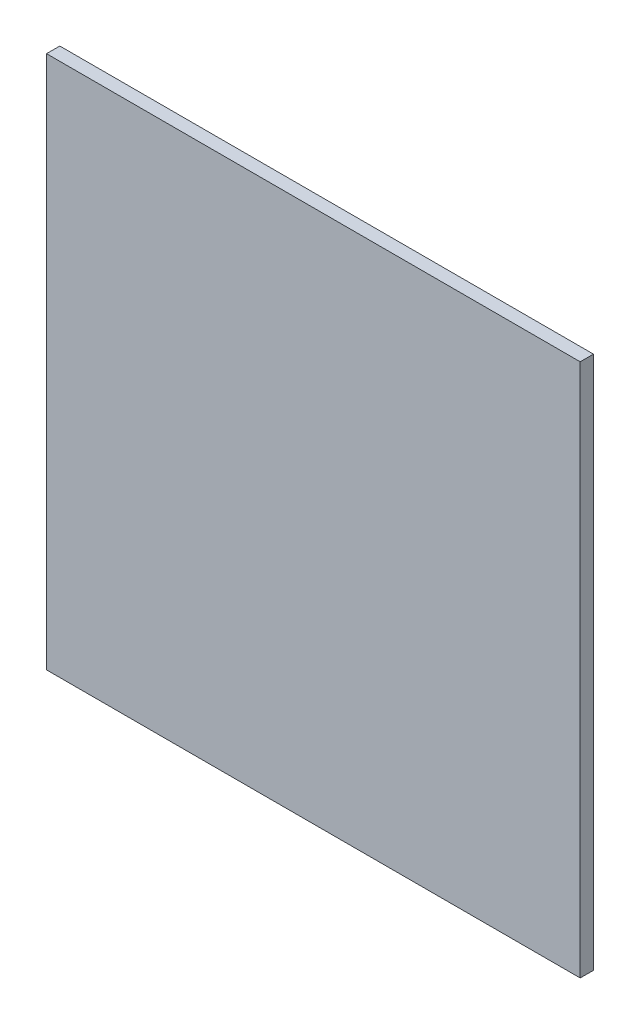
SolidWorks part; units mm, degrees
ref_plane "Front Plane" through (0, 0, 0) normal (0, 0, 1) x (1, 0, 0)
ref_plane "Top Plane" through (0, 0, 0) normal (0, 1, 0) x (1, 0, 0)
ref_plane "Right Plane" through (0, 0, 0) normal (1, 0, 0) x (0, 0, -1)
sketch "Sketch1" plane through (0, 0, 0) normal (0, 0, 1) x (1, 0, 0)
  line L1 (-63.881, -63.881) -> (63.881, -63.881)
  line L2 (-63.881, -63.881) -> (-63.881, 63.881)
  line L3 (-63.881, 63.881) -> (63.881, 63.881)
  line L4 (63.881, -63.881) -> (63.881, 63.881)
  line L5 (-63.881, -63.881) -> (63.881, 63.881) construction
  line L6 (-63.881, 63.881) -> (63.881, -63.881) construction
  point P0 (0, 0)
  dimension "D1" = 127.762
  dimension "D2" = 127.762
extrude "Boss-Extrude1" add sketch "Sketch1" along normal blind 3.175
